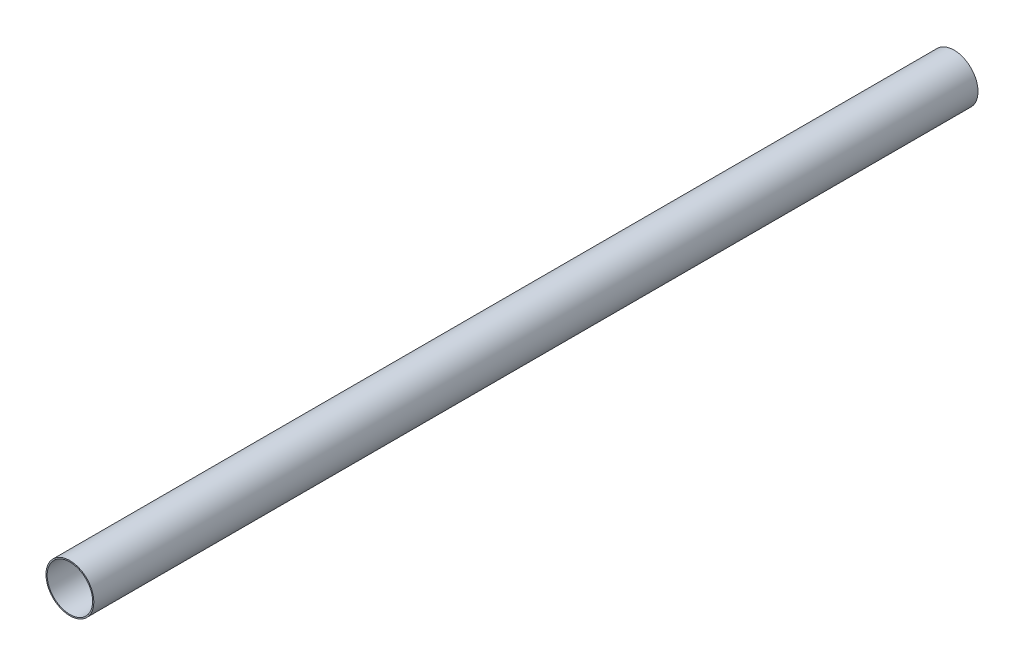
SolidWorks part; units mm, degrees
ref_plane "Front Plane" through (0, 0, 0) normal (0, 0, 1) x (1, 0, 0)
ref_plane "Top Plane" through (0, 0, 0) normal (0, 1, 0) x (1, 0, 0)
ref_plane "Right Plane" through (0, 0, 0) normal (1, 0, 0) x (0, 0, -1)
sketch "Sketch1" plane through (0, 0, 0) normal (0, 0, 1) x (1, 0, 0)
  circle A0 centre (0, 0) radius 15.265
  circle A1 centre (0, 0) radius 14.505
  dimension "D1" = 0.76
extrude "Boss-Extrude1" add sketch "Sketch1" along normal blind 563.88
sketch "Sketch3" plane through (0, 0, 0) normal (0, 1, 0) x (1, 0, 0)
  line L0 (0, -2.9772) -> (0, -662.247) construction
